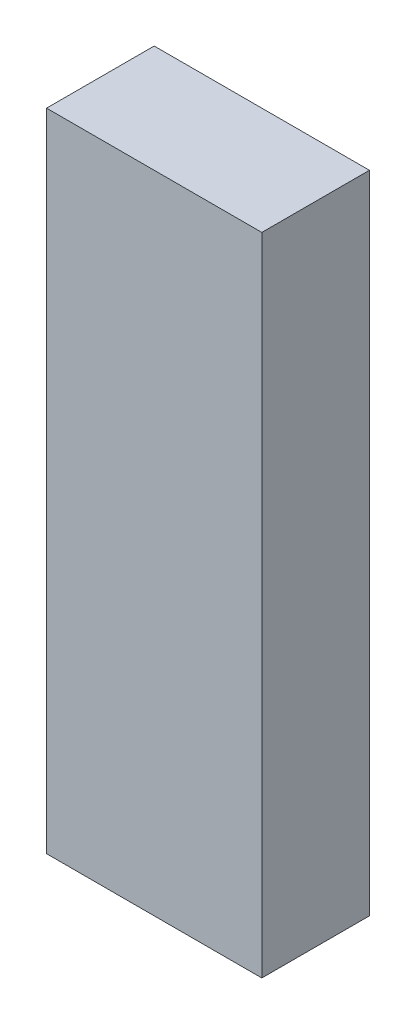
SolidWorks part; units mm, degrees
ref_plane "Front" through (0, 0, 0) normal (0, 0, 1) x (1, 0, 0)
ref_plane "Top" through (0, 0, 0) normal (0, 1, 0) x (1, 0, 0)
ref_plane "Right" through (0, 0, 0) normal (1, 0, 0) x (0, 0, -1)
sketch "Sketch1" plane through (0, 0, 0) normal (0, 0, 1) x (1, 0, 0)
  line L1 (0, 0) -> (10, 0)
  line L2 (0, 0) -> (0, 30)
  line L3 (0, 30) -> (10, 30)
  line L4 (10, 0) -> (10, 30)
  dimension "D1" = 10
  dimension "D2" = 30
extrude "Boss-Extrude1" add sketch "Sketch1" along normal blind 5
